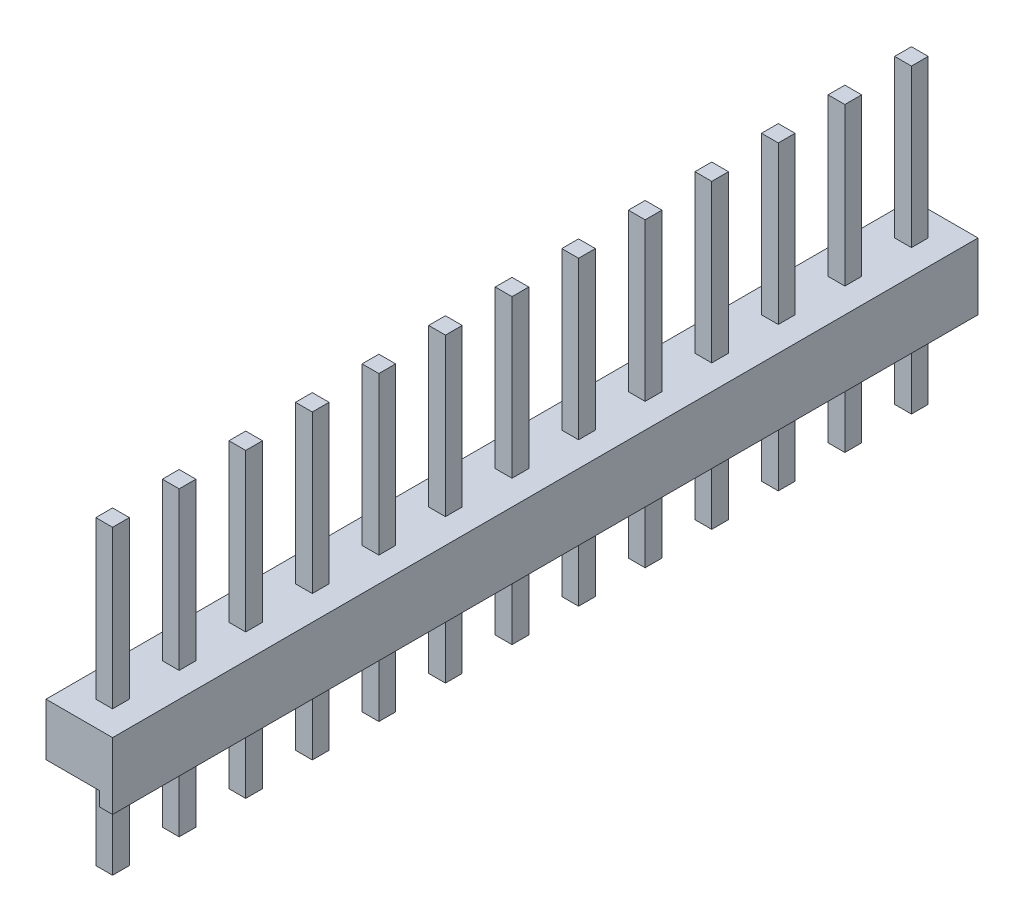
SolidWorks part; units mm, degrees
ref_plane "Спереди" through (0, 0, 0) normal (0, 0, 1) x (1, 0, 0)
ref_plane "Сверху" through (0, 0, 0) normal (0, 1, 0) x (1, 0, 0)
ref_plane "Справа" through (0, 0, 0) normal (1, 0, 0) x (0, 0, -1)
sketch "Эскиз1" plane through (0, 0, 0) normal (0, 0, 1) x (1, 0, 0)
  line L0 (-2.54, 0) -> (-2.54, 2.54)
  line L1 (-2.54, 2.54) -> (2.54, 2.54)
  line L2 (2.54, 2.54) -> (2.54, 0)
  line L3 (-2.54, 0) -> (-2.04, 0)
  line L4 (-2.04, 0) -> (-2.04, 0.54)
  line L5 (-2.04, 0.54) -> (2.04, 0.54)
  line L6 (2.04, 0.54) -> (2.04, 0)
  line L7 (2.04, 0) -> (2.54, 0)
  line L8 (-2.54, 0) -> (2.54, 0) construction
  dimension "D1" = 2.54
  dimension "D2" = 5.08
  dimension "D3" = 0.5
  dimension "D4" = 0.54
  dimension "D5" = 0.5
  dimension "D6" = 2.54
extrude "Бобышка-Вытянуть1" add sketch "Эскиз1" along normal blind 2.54
sketch "Эскиз2" plane through (0, 2.54, 0) normal (0, 1, 0) x (1, 0, 0)
  line L0 (-2.54, -1.27) -> (2.54, -1.27) construction
  line L1 (-1.59, -0.95) -> (-0.95, -0.95)
  line L2 (-1.59, -0.95) -> (-1.59, -1.59)
  line L3 (-1.59, -1.59) -> (-0.95, -1.59)
  line L4 (-0.95, -0.95) -> (-0.95, -1.59)
  line L5 (0.95, -0.95) -> (1.59, -0.95)
  line L6 (0.95, -0.95) -> (0.95, -1.59)
  line L7 (0.95, -1.59) -> (1.59, -1.59)
  line L8 (1.59, -0.95) -> (1.59, -1.59)
  line L9 (-2.54, -2.54) -> (-2.54, 0) construction
  line L12 (0, 0) -> (0, -2.54) construction
  line L13 (2.54, -2.54) -> (-2.54, -2.54) construction
  line L14 (2.54, -2.54) -> (2.54, 0) construction
  line L15 (-1.27, -1.59) -> (-1.27, -0.95) construction
  line L16 (1.27, -0.95) -> (1.27, -1.59) construction
  dimension "D1" = 0.64
  dimension "D2" = 2.54
extrude "Бобышка-Вытянуть2" add sketch "Эскиз2" along normal blind 6 and the other way blind 5.5
pattern_linear "Линейный массив27" count 13 spacing 2.54 along (0, 0, -1) of "Бобышка-Вытянуть1", "Бобышка-Вытянуть2"
sketch "Croquis1" plane through (0, 0, 0) normal (0, 1, 0) x (1, 0, 0)
  line L0 (0, -2.54) -> (0, 30.48)
  line L1 (2.54, -2.54) -> (-2.54, -2.54) construction
  line L2 (2.54, 30.48) -> (-2.54, 30.48) construction
  line L3 (0, 30.48) -> (-6.1148, 30.48)
  line L4 (-6.1148, 30.48) -> (-6.1148, -2.54)
  line L5 (-6.1148, -2.54) -> (0, -2.54)
extrude "Cortar-Extruir1" cut sketch "Croquis1" against normal through all both and the other way through all
